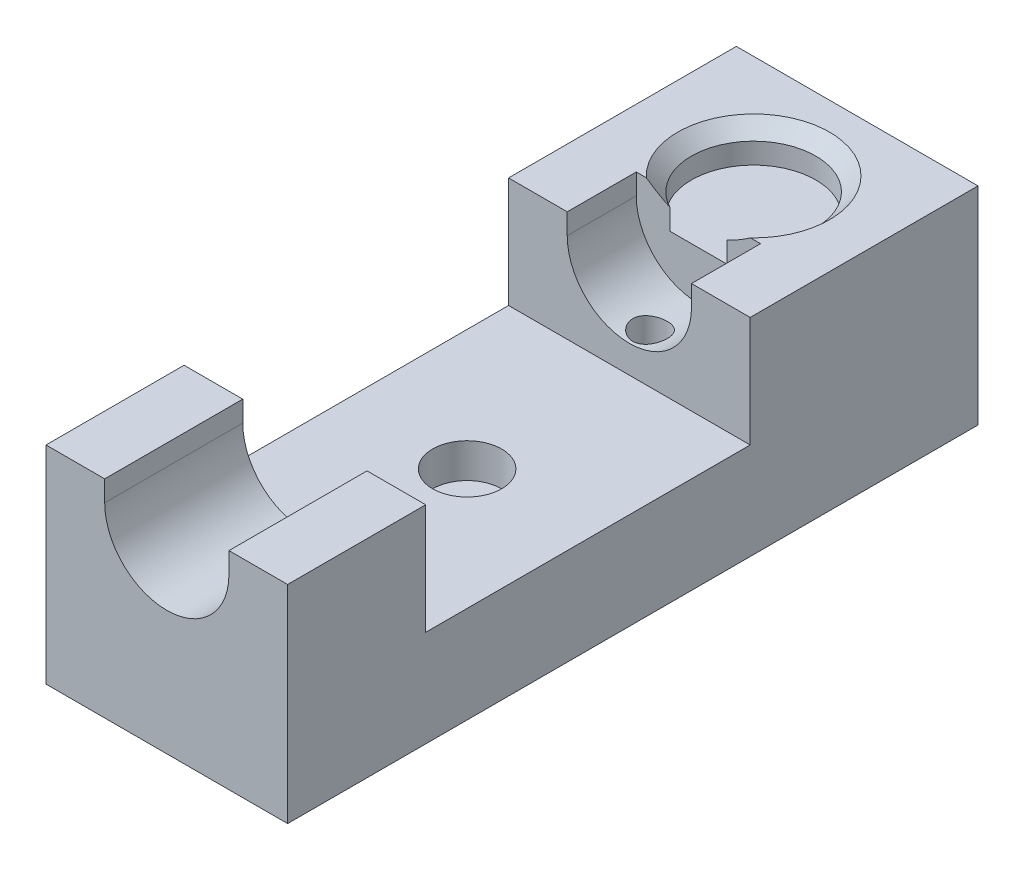
SolidWorks part; units mm, degrees
ref_plane "前视基准面" through (0, 0, 0) normal (0, 0, 1) x (1, 0, 0)
ref_plane "上视基准面" through (0, 0, 0) normal (0, 1, 0) x (1, 0, 0)
ref_plane "右视基准面" through (0, 0, 0) normal (1, 0, 0) x (0, 0, -1)
sketch "草图1" plane through (0, 0, 0) normal (0, 1, 0) x (1, 0, 0)
  line L1 (17.5, -50) -> (-17.5, -50)
  line L2 (17.5, -50) -> (17.5, 50)
  line L3 (17.5, 50) -> (-17.5, 50)
  line L4 (-17.5, -50) -> (-17.5, 50)
  line L5 (17.5, -50) -> (-17.5, 50) construction
  line L6 (17.5, 50) -> (-17.5, -50) construction
  point P0 (0, 0)
  dimension "D1" = 35
  dimension "D2" = 100
extrude "凸台-拉伸1" add sketch "草图1" along normal blind 30
sketch "草图2" plane through (0, 30, 0) normal (0, 1, 0) x (1, 0, 0)
  line L0 (0, 50) -> (0, 35) construction
  line L1 (17.5, 50) -> (-17.5, 50) construction
  circle A0 centre (0, 35) radius 9
  dimension "D1" = 18
  dimension "D2" = 15
extrude "切除-拉伸1" cut sketch "草图2" against normal blind 5
chamfer "倒角1" distance 2 angle 45 1 edges at (0, 30, -26)
sketch "草图3" plane through (0, 0, 50) normal (0, 0, 1) x (1, 0, 0)
  line L0 (0, 33) -> (0, 27) construction
  line L1 (-17.5, 30) -> (17.5, 30) construction
  line L2 (9, 33) -> (9, 27)
  line L3 (-9, 33) -> (-9, 27)
  arc A0 (9, 33) -> (-9, 33) centre (0, 33) ccw
  arc A1 (-9, 27) -> (9, 27) centre (0, 27) ccw
  point P5 (0, 30)
  dimension "D1" = 9
  dimension "D2" = 3
extrude "切除-拉伸3" cut sketch "草图3" against normal offset from surface (77 mm away) 23 up to face at (0, 15, -50)
sketch "草图4" plane through (0, 30, 0) normal (0, 1, 0) x (1, 0, 0)
  line L0 (-17.5, 50) -> (-17.5, -50) construction
  line L1 (-17.5, 17) -> (17.5, 17)
  line L2 (-17.5, 17) -> (-17.5, -30)
  line L3 (-17.5, -30) -> (17.5, -30)
  line L4 (17.5, 17) -> (17.5, -30)
  line L5 (17.5, -50) -> (17.5, 50) construction
  line L6 (7.5498, 27) -> (9, 27) construction
  line L7 (9, -50) -> (17.5, -50) construction
  dimension "D1" = 10
  dimension "D2" = 20
extrude "切除-拉伸4" cut sketch "草图4" against normal blind 16
sketch "草图5" plane through (0, 0, 0) normal (0, 1, 0) x (1, 0, 0)
  line L0 (0, 0) -> (0, 20) construction
  line L1 (0, 0) -> (-26.8991, 0) construction
  circle A0 centre (0, 20) radius 3.25
  circle A1 centre (0, -20) radius 3.25
  dimension "D1" = 40
  dimension "D2" = 6.5
hole_wizard "M6 螺纹孔1" positions "3D草图1" profile "草图6" tap size "M6" standard "Iso" end condition through all
sketch3d "3D草图1"
  point P0 (0, 0, -20)
  point P3 (0, 0, 20)
sketch "草图6" plane through (0, 0, -20) normal (1, 0, 0) x (0, 0, -1)
  line L0 (0, 0) -> (0, 30)
  line L1 (0, 30) -> (2.5, 30)
  line L2 (2.5, 30) -> (2.5, 0)
  line L5 (2.5, 0) -> (0, 0)
  line L11 (0, -6.35) -> (0, 107.95) construction
  dimension "螺纹线主直径" = 5
  dimension "通孔螺纹孔钻头深度" = 30
sketch "草图7" plane through (0, 14, 0) normal (0, 1, 0) x (1, 0, 0)
  line L0 (0, 17) -> (0, -30) construction
  line L1 (17.5, 17) -> (-17.5, 17) construction
  line L2 (-17.5, -30) -> (17.5, -30) construction
  circle A0 centre (0, -6.5) radius 5
  dimension "D1" = 10
extrude "切除-拉伸5" cut sketch "草图7" against normal blind 5
